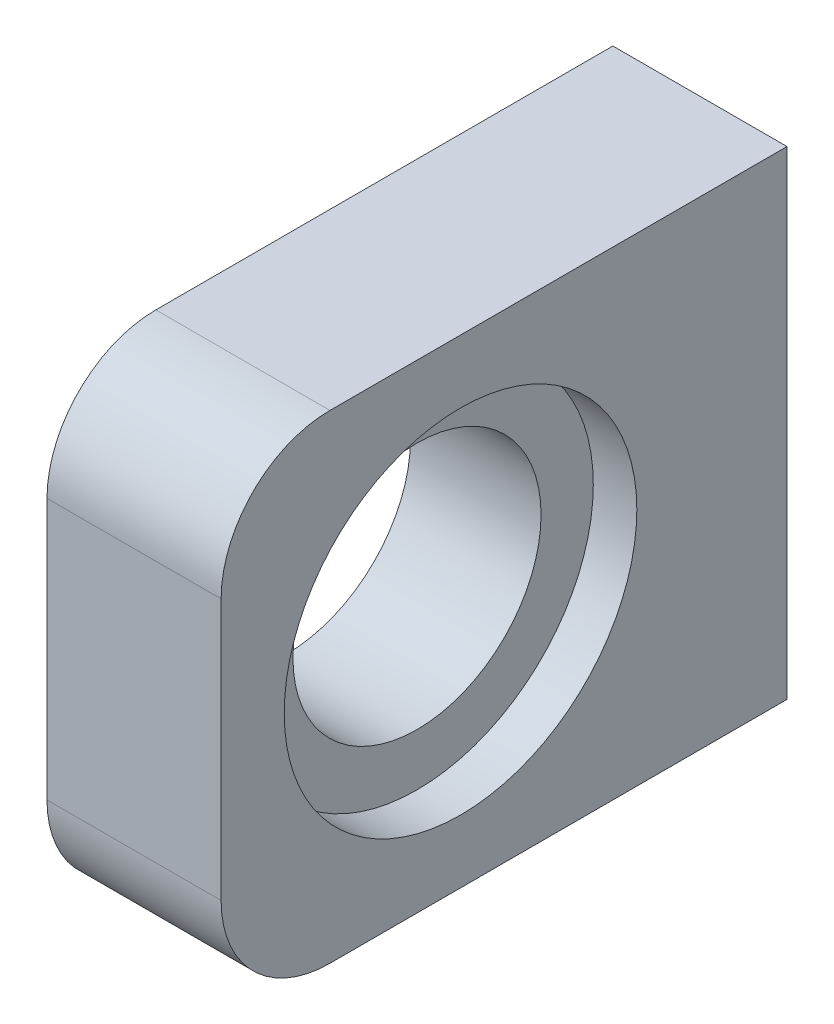
SolidWorks part; units mm, degrees
ref_plane "Front Plane" through (0, 0, 0) normal (0, 0, 1) x (1, 0, 0)
ref_plane "Top Plane" through (0, 0, 0) normal (0, 1, 0) x (1, 0, 0)
ref_plane "Right Plane" through (0, 0, 0) normal (1, 0, 0) x (0, 0, -1)
ref_plane "Plane1" through (8, 0, 0) normal (1, 0, 0) x (0, 0, -1)
sketch "Sketch1" plane through (8, 0, 0) normal (1, 0, 0) x (0, 0, -1)
  line L0 (-22, 22) -> (-22, 0)
  line L1 (-22, 0) -> (4, 0)
  line L2 (4, 0) -> (4, 22)
  line L3 (4, 22) -> (-22, 22)
extrude "Boss-Extrude1" add sketch "Sketch1" against normal blind 8
sketch "Sketch2" plane through (8, 0, 0) normal (1, 0, 0) x (0, 0, -1)
  line L0 (-22, 22) -> (-22, 0) construction
  circle A0 centre (-11, 11) radius 8.1
  point P4 (-22, 11)
  dimension "D1" = 11
extrude "Cut-Extrude1" cut sketch "Sketch2" against normal blind 2
hole_wizard "Ø3.3 (3.3) Diameter Hole1" positions "Sketch4" profile "Sketch3" hole size "Ø3.3" standard "ANSI Metric"
sketch "Sketch4" plane through (0, 0, -4) normal (0, 0, -1) x (-1, 0, 0)
  point P0 (-4, 16)
  point P1 (-4, 6)
sketch "Sketch3" plane through (4, 16, -4) normal (1, 0, 0) x (0, 1, 0)
  line L0 (0, 0) -> (0, 6.9914)
  line L1 (0, 6.9914) -> (1.65, 6)
  line L2 (1.65, 6) -> (1.65, 0)
  line L5 (1.65, 0) -> (0, 0)
  line L10 (0, 6.9914) -> (-1.65, 6) construction
  line L11 (0, -6.35) -> (0, 107.95) construction
  dimension "Hole Dia." = 3.3
  dimension "Hole Depth" = 6
  dimension "Drill Angle" = 118
hole_wizard "M10 Clearance Hole1" positions "Sketch6" profile "Sketch5" hole size "M10" standard "ANSI Metric" end condition through all
sketch "Sketch6" plane through (6, 0, 0) normal (1, 0, 0) x (0, 0, -1)
  point P0 (-11, 11)
sketch "Sketch5" plane through (6, 11, 11) normal (0, 1, 0) x (0, 0, -1)
  line L0 (0, 0) -> (0, 6)
  line L1 (0, 6) -> (5.7, 6)
  line L2 (5.7, 6) -> (5.7, 0)
  line L5 (5.7, 0) -> (0, 0)
  line L11 (0, -6.35) -> (0, 107.95) construction
  dimension "Thru Hole Dia." = 11.4
  dimension "Thru Hole Depth" = 6
fillet "Fillet1" radius 5 2 edges at (4, 22, 22) (4, 0, 22)
